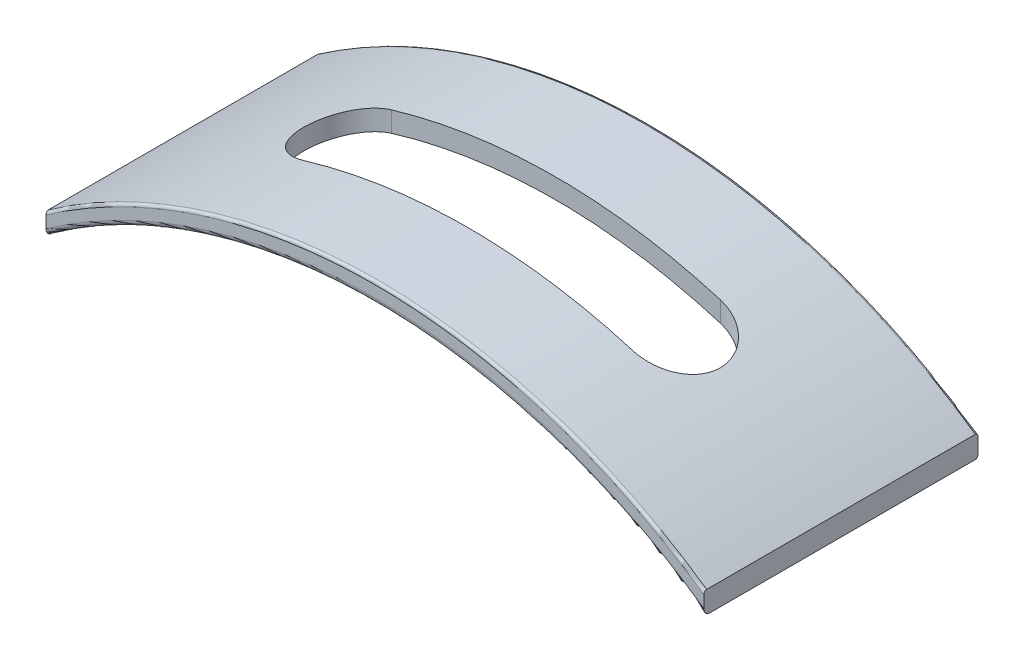
SolidWorks part; units mm, degrees
material "AISI 1020 Steel, Cold Rolled"
ref_plane "Front Plane" through (0, 0, 0) normal (0, 0, 1) x (1, 0, 0)
ref_plane "Top Plane" through (0, 0, 0) normal (0, 1, 0) x (1, 0, 0)
ref_plane "Right Plane" through (0, 0, 0) normal (1, 0, 0) x (0, 0, -1)
sketch "Sketch1" plane through (0, 0, 0) normal (0, 0, 1) x (1, 0, 0)
  line L0 (-30, 0) -> (-30, -2)
  line L1 (30, 0) -> (30, -2)
  arc A0 (-30, 0) -> (30, 0) centre (0, -42.9013) cw
  arc A1 (-30, -2) -> (30, -2) centre (0, -43.9013) cw
  point P4 (0, 0)
  dimension "D1" = 60
  dimension "D4" = 1
  dimension "D2" = 2
  dimension "D3" = 2
extrude "Boss-Extrude1" add sketch "Sketch1" along normal blind 25 contours A0 L1 A1 L0
fillet "Fillet2" radius 0.25 1 edges at (0, 9.4487, 25)
fillet "Fillet3" radius 0.5 1 edges at (0, 7.6324, 25)
fillet "Fillet5" radius 0.25 2 edges at (0, 7.6324, 0) (0, 9.4487, 0)
sketch "Sketch6" plane through (0, 0, 0) normal (0, 1, 0) x (1, 0, 0)
  line L0 (-15, -12.5) -> (15, -12.5) construction
  line L1 (-15, -8.5) -> (15, -8.5)
  line L2 (-15, -16.5) -> (15, -16.5)
  line L3 (-55, 0) -> (55, 0) construction
  line L4 (-30, -24.75) -> (-30, -0.25) construction
  arc A0 (-15, -8.5) -> (-15, -16.5) centre (-15, -12.5) ccw
  arc A1 (15, -16.5) -> (15, -8.5) centre (15, -12.5) ccw
  point P2 (0, -12.5)
  dimension "D2" = 4
  dimension "D4" = 15
  dimension "D1" = 12.5
  dimension "D3" = 30
extrude "Cut-Extrude2" cut sketch "Sketch6" along normal through all
